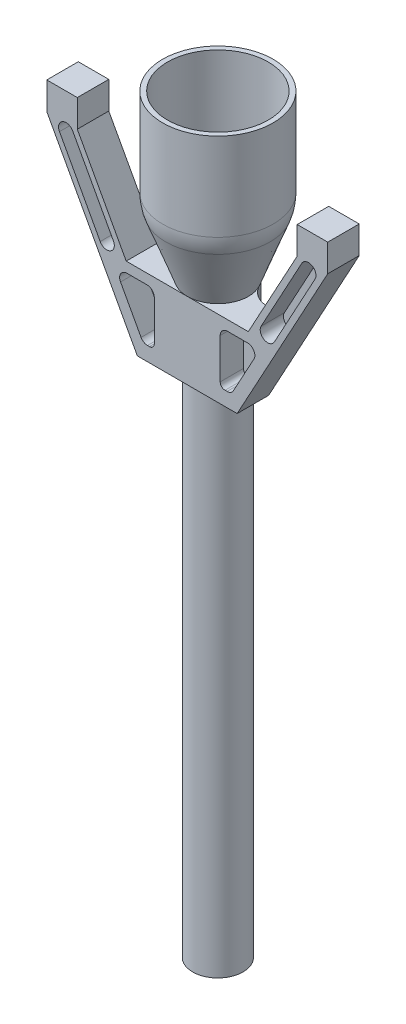
SolidWorks part; units mm, degrees
ref_plane "Front Plane" through (0, 0, 0) normal (0, 0, 1) x (1, 0, 0)
ref_plane "Top Plane" through (0, 0, 0) normal (0, 1, 0) x (1, 0, 0)
ref_plane "Right Plane" through (0, 0, 0) normal (1, 0, 0) x (0, 0, -1)
sketch "Sketch1" plane through (0, 0, 0) normal (0, 1, 0) x (1, 0, 0)
  circle A0 centre (0, 0) radius 5.2
  circle A1 centre (0, 0) radius 4.65
  dimension "D1" = 10.4
  dimension "D2" = 9.3
extrude "Boss-Extrude1" add sketch "Sketch1" along normal blind 121.35
ref_plane "Plane1" through (0, 121.35, 0) normal (0, 1, 0) x (1, 0, 0)
sketch "Sketch2" plane through (0, 121.35, 0) normal (0, 1, 0) x (1, 0, 0)
  line L0 (-6.3619, 0) -> (7.5553, 0) construction
  line L1 (0, 0) -> (0, 6.2984) construction
  line L2 (0, 6.2984) -> (0, -7.2152) construction
  circle A0 centre (0, 0) radius 6.32
  circle A1 centre (0, 0) radius 4.65
  dimension "D1" = 9.3
  dimension "D2" = 12.64
extrude "Boss-Extrude2" add sketch "Sketch2" against normal blind 15.8
ref_axis "Axis1" through (0, 121.35, 0) along (0, -1, 0)
sketch "Sketch3" plane through (0, 0, 0) normal (0, 0, 1) x (1, 0, 0)
  line L0 (-6.32, 121.35) -> (-11.4, 135)
  line L1 (-11.4, 135) -> (-10.4, 135)
  line L2 (-10.4, 135) -> (-4.65, 121.35)
  line L3 (-4.65, 121.35) -> (-6.32, 121.35)
  dimension "D1" = 1
  dimension "D2" = 13.65
  dimension "D3" = 5.08
revolve "Revolve1" add sketch "Sketch3" angle 360 about axis through (0, 121.35, 0) along (0, -1, 0)
ref_plane "Plane4" through (0, 135, 0) normal (0, 1, 0) x (1, 0, 0)
sketch "Sketch4" plane through (0, 135, 0) normal (0, 1, 0) x (1, 0, 0)
  line L0 (-12.8793, 0) -> (14.2139, 0) construction
  line L1 (0, -11.4) -> (0, 11.4) construction
  circle A0 centre (0, 0) radius 11.4 construction
  circle A1 centre (0, 0) radius 11.4
  circle A2 centre (0, 0) radius 10.4
  dimension "D1" = 20.8
extrude "Boss-Extrude3" add sketch "Sketch4" along normal blind 19.9
ref_plane "Plane5" through (0, 0, 6.32) normal (0, 0, 1) x (1, 0, 0)
sketch "Sketch6" plane through (0, 0, 6.32) normal (0, 0, 1) x (1, 0, 0)
  line L0 (0, 122.1602) -> (0, 104.5293) construction
  line L1 (-10.3, 105.55) -> (10.3, 105.55)
  line L2 (-5.2, 105.55) -> (5.2, 105.55) construction
  line L3 (10.3, 105.55) -> (29, 139.89)
  line L4 (29, 139.89) -> (29, 145.55)
  line L5 (29, 145.55) -> (22.7, 145.55)
  line L6 (22.7, 145.55) -> (22.7, 139.89)
  line L7 (22.7, 139.89) -> (12.604, 121.35)
  line L8 (12.54, 121.35) -> (-12.54, 121.35) construction
  line L9 (12.604, 121.35) -> (-12.604, 121.35)
  line L16 (-29, 139.89) -> (-29, 145.55)
  line L21 (-29, 145.55) -> (-22.7, 145.55)
  line L22 (-22.7, 145.55) -> (-22.7, 139.89)
  line L23 (-22.7, 139.89) -> (-12.604, 121.35)
  line L24 (-10.3, 105.55) -> (-29, 139.89)
  point P14 (0, 105.55)
  point P25 (22.7, 139.89)
  point P37 (6.8, 119.35)
  point P61 (0, 121.35)
  dimension "D1" = 15.8
  dimension "D2" = 40
  dimension "D3" = 6.3
  dimension "D4" = 10.3
  dimension "D7" = 5.66
  dimension "D8" = 29
extrude "Boss-Extrude4" add sketch "Sketch6" against normal blind 6.5 separate body
sketch "Sketch7" plane through (0, 0, 6.32) normal (0, 0, 1) x (1, 0, 0)
  line L0 (0, 122.264) -> (0, 102.9791) construction
  line L1 (8.3, 119.2576) -> (12.4561, 119.2576)
  line L2 (13.7736, 117.0407) -> (9.5341, 109.2496)
  line L3 (8.2165, 108.4666) -> (7.8, 108.4666)
  line L4 (6.8, 109.4666) -> (6.8, 117.7576)
  line L5 (-16.611, 122.9122) -> (-25.0157, 138.3578) construction
  line L6 (-15.2486, 123.6536) -> (-23.6534, 139.0991)
  line L7 (-17.9733, 122.1709) -> (-26.378, 137.6164)
  line L8 (-25.85, 139.89) -> (-15.3017, 120.5194) construction
  line L10 (22.7, 139.89) -> (29, 139.89) construction
  line L11 (25.85, 139.89) -> (15.3017, 120.5194) construction
  line L12 (10.3, 105.55) -> (29, 139.89) construction
  line L13 (16.611, 122.9122) -> (25.0157, 138.3578) construction
  line L14 (15.2486, 123.6536) -> (23.6534, 139.0991)
  line L15 (17.9733, 122.1709) -> (26.378, 137.6164)
  line L16 (-8.2165, 108.4666) -> (-7.8, 108.4666)
  line L17 (-8.3, 119.2576) -> (-12.4561, 119.2576)
  line L18 (-13.7736, 117.0407) -> (-9.5341, 109.2496)
  line L19 (-6.8, 109.4666) -> (-6.8, 117.7576)
  arc A0 (6.8, 117.7576) -> (8.3, 119.2576) centre (8.3, 117.7576) cw
  arc A1 (13.7736, 117.0407) -> (12.4561, 119.2576) centre (12.4561, 117.7576) ccw
  arc A2 (15.2486, 123.6536) -> (17.9733, 122.1709) centre (16.611, 122.9122) ccw
  arc A3 (26.378, 137.6164) -> (23.6534, 139.0991) centre (25.0157, 138.3578) ccw
  arc A4 (9.5341, 109.2496) -> (8.2165, 108.4666) centre (8.2165, 109.9666) cw
  arc A5 (6.8, 109.4666) -> (7.8, 108.4666) centre (7.8, 109.4666) ccw
  arc A6 (-15.2486, 123.6536) -> (-17.9733, 122.1709) centre (-16.611, 122.9122) cw
  arc A7 (-26.378, 137.6164) -> (-23.6534, 139.0991) centre (-25.0157, 138.3578) cw
  arc A8 (-9.5341, 109.2496) -> (-8.2165, 108.4666) centre (-8.2165, 109.9666) ccw
  arc A9 (-6.8, 109.4666) -> (-7.8, 108.4666) centre (-7.8, 109.4666) cw
  arc A10 (-6.8, 117.7576) -> (-8.3, 119.2576) centre (-8.3, 117.7576) ccw
  arc A11 (-13.7736, 117.0407) -> (-12.4561, 119.2576) centre (-12.4561, 117.7576) cw
  point P20 (20.8133, 130.635)
  point P33 (-20.8133, 130.635)
  dimension "D2" = 1.5
  dimension "D3" = 1.5
  dimension "D4" = 1.5
  dimension "D5" = 1
  dimension "D1" = 6.8
extrude "Cut-Extrude1" cut sketch "Sketch7" against normal blind 4.8
fillet "Fillet2" radius 10 1 edges at (0, 135, 11.4)
sketch "Sketch8" plane through (0, 0, 0) normal (0, 1, 0) x (1, 0, 0)
  circle A0 centre (0, 0) radius 4.65
  dimension "D1" = 9.3
extrude "Cut-Extrude2" cut sketch "Sketch8" along normal through all both and the other way through all
combine bodies "Combine1" operation type add bodies to combine 109 104
fillet "Fillet3" radius 5 1 edges at (-6.3174, 113.45, -0.18)
fillet "Fillet4" radius 5 1 edges at (6.3174, 113.45, -0.18)
